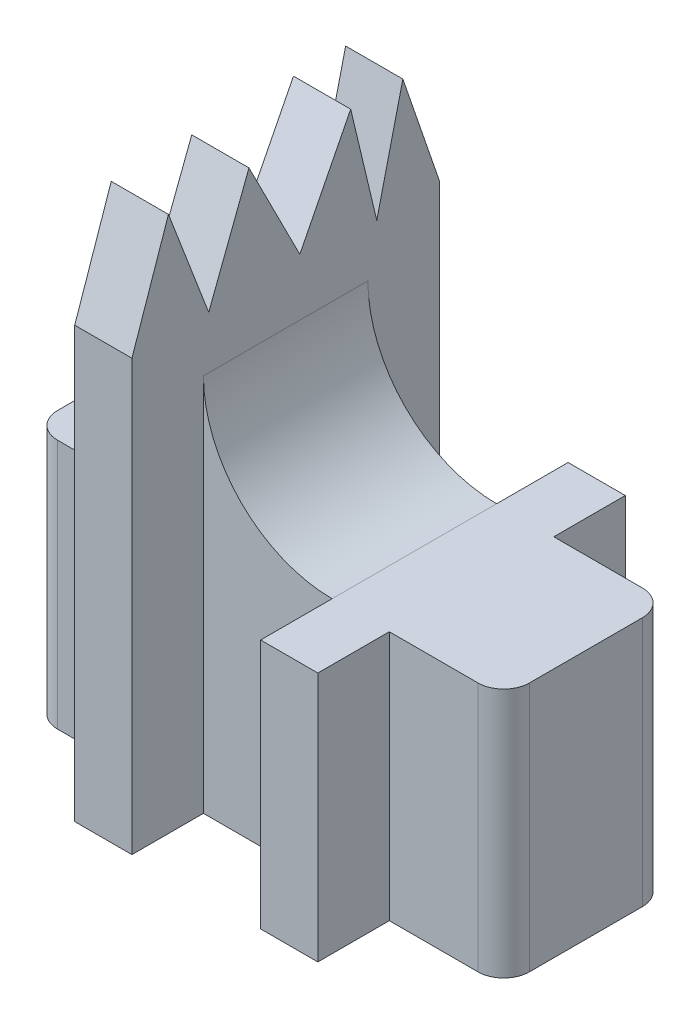
SolidWorks part; units mm, degrees
ref_plane "Front Plane" through (0, 0, 0) normal (0, 0, 1) x (1, 0, 0)
ref_plane "Top Plane" through (0, 0, 0) normal (0, 1, 0) x (1, 0, 0)
ref_plane "Right Plane" through (0, 0, 0) normal (1, 0, 0) x (0, 0, -1)
sketch "Sketch1" plane through (0, 0, 0) normal (0, 1, 0) x (1, 0, 0)
  line L0 (-8.25, 0) -> (8.25, 0) construction
  line L1 (-8.25, -2.875) -> (8.25, -2.875)
  line L2 (-8.25, -2.875) -> (-8.25, 2.875)
  line L3 (-8.25, 2.875) -> (8.25, 2.875)
  line L5 (-8.25, -2.875) -> (0, 0) construction
  line L6 (-8.25, 2.875) -> (0, 0) construction
  line L7 (0, 2.875) -> (0, -2.875)
  line L8 (-4.25, -5.375) -> (-2.25, -5.375)
  line L9 (-4.25, -5.375) -> (-4.25, 5.375)
  line L10 (-4.25, 5.375) -> (-2.25, 5.375)
  line L11 (-2.25, -5.375) -> (-2.25, 5.375)
  line L12 (-4.25, -5.375) -> (-2.25, 5.375) construction
  line L13 (-4.25, 5.375) -> (-2.25, -5.375) construction
  line L18 (4.25, 5.375) -> (2.25, -5.375) construction
  line L19 (4.25, -5.375) -> (2.25, 5.375) construction
  line L20 (8.25, 2.875) -> (0, 0) construction
  line L21 (8.25, -2.875) -> (0, 0) construction
  line L22 (2.25, -5.375) -> (2.25, 5.375)
  line L23 (4.25, 5.375) -> (2.25, 5.375)
  line L24 (4.25, -5.375) -> (4.25, 5.375)
  line L25 (4.25, -5.375) -> (2.25, -5.375)
  line L26 (8.25, -2.875) -> (8.25, 2.875)
  point P0 (0, 0)
  point P8 (-3.25, 0)
  point P22 (3.25, 0)
  dimension "D1" = 2.25
  dimension "D2" = 2.5
  dimension "D3" = 5.75
  dimension "D4" = 4
  dimension "D5" = 2
extrude "Boss-Extrude1" add sketch "Sketch1" along normal blind 8.75 contours L1 L9 L3 L2 | L3 L11 L10 L9 | L8 L11 L1 L9 | L1 L11 L3 L9 | L11 L1 L7 L3 | L1 L22 L3 L7 | L3 L24 L23 L22 | L1 L26 L3 L24 | L1 L24 L3 L22 | L25 L24 L1 L22
fillet "Fillet1" radius 0.9 4 edges at (8.25, 4.375, -2.875) (8.25, 4.375, 2.875) (-8.25, 4.375, 2.875) (-8.25, 4.375, -2.875)
sketch "Sketch2" plane through (0, 8.75, 0) normal (0, 1, 0) x (1, 0, 0)
  line L1 (-4.25, 5.375) -> (-2.25, 5.375)
  line L2 (-4.25, 5.375) -> (-4.25, -5.375)
  line L3 (-4.25, -5.375) -> (-2.25, -5.375)
  line L4 (-2.25, 5.375) -> (-2.25, -5.375)
extrude "Boss-Extrude2" add sketch "Sketch2" along normal blind 10
sketch "Sketch3" plane through (-4.25, 0, 0) normal (-1, 0, 0) x (0, 0, 1)
  line L0 (-5.375, 15.0317) -> (-4.0979, 18.75)
  line L1 (-5.375, 15.0317) -> (-5.375, 18.75)
  line L2 (-5.375, 18.75) -> (5.375, 18.75)
  line L3 (5.375, 18.75) -> (5.375, 15.0317)
  line L6 (-5.375, 18.75) -> (-5.375, 0) construction
  line L7 (-5.375, 18.75) -> (5.375, 18.75) construction
  line L8 (-4.0979, 18.75) -> (-3.1857, 14.9258)
  line L10 (-3.1857, 14.9258) -> (-2.2736, 18.75)
  line L11 (-2.2736, 18.75) -> (-0.4955, 15.2436)
  line L12 (-0.4955, 15.2436) -> (1.2827, 18.75)
  line L13 (1.2827, 18.75) -> (2.6903, 15.0791)
  line L15 (2.6903, 15.0791) -> (4.0979, 18.75)
  line L16 (4.0979, 18.75) -> (5.375, 15.0317)
  line L17 (5.375, 18.75) -> (5.375, 0) construction
  line M16 (5.375, 0) -> (5.375, 18.75)
  line M17 (5.375, 18.75) -> (-5.375, 18.75)
  line M18 (-5.375, 18.75) -> (-5.375, 0)
extrude "Cut-Extrude1" cut sketch "Sketch3" against normal through all contours L0 M18 M17 | L8 L10 L2 | L11 L12 L2 | L13 L15 L2 | L16 M17 M16
fillet "Fillet2" radius 4.5 1 edges at (-2.25, 8.75, 0)
